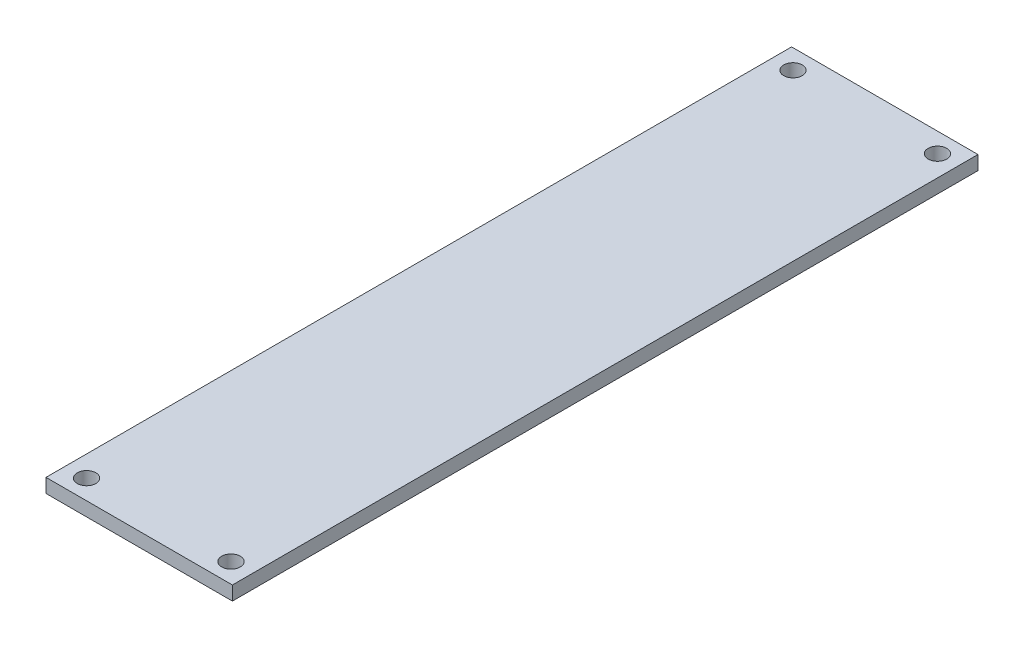
SolidWorks part; units mm, degrees
ref_plane "Front Plane" through (0, 0, 0) normal (0, 0, 1) x (1, 0, 0)
ref_plane "Top Plane" through (0, 0, 0) normal (0, 1, 0) x (1, 0, 0)
ref_plane "Right Plane" through (0, 0, 0) normal (1, 0, 0) x (0, 0, -1)
sketch "Sketch1" plane through (0, 0, 0) normal (0, 1, 0) x (1, 0, 0)
  line L1 (0, 0) -> (20, 0)
  line L2 (0, 0) -> (0, 80)
  line L3 (0, 80) -> (20, 80)
  line L4 (20, 0) -> (20, 80)
  dimension "D1" = 80
  dimension "D2" = 20
extrude "Boss-Extrude1" add sketch "Sketch1" along normal blind 1.5
sketch "Sketch2" plane through (0, 1.5, 0) normal (0, 1, 0) x (1, 0, 0)
  line L0 (2.25, 77.9) -> (17.75, 2.1) construction
  line L1 (2.25, 77.9) -> (17.75, 77.9) construction
  line L2 (2.25, 77.9) -> (2.25, 2.1) construction
  line L3 (2.25, 2.1) -> (17.75, 2.1) construction
  line L4 (17.75, 77.9) -> (17.75, 2.1) construction
  line L5 (20, 0) -> (0, 80) construction
  circle A0 centre (2.25, 77.9) radius 1
  circle A1 centre (17.75, 77.9) radius 1
  circle A2 centre (2.25, 2.1) radius 1
  circle A3 centre (17.75, 2.1) radius 1
  point P12 (10, 40)
  dimension "D1" = 2
  dimension "D2" = 15.5
  dimension "D3" = 75.8
extrude "Cut-Extrude1" cut sketch "Sketch2" against normal through all
